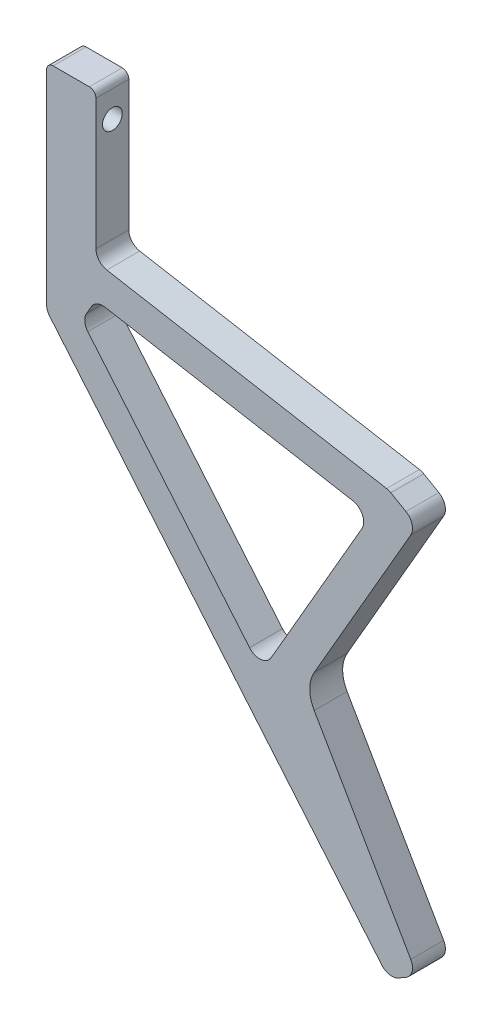
SolidWorks part; units mm, degrees
ref_plane "Front Plane" through (0, 0, 0) normal (0, 0, 1) x (1, 0, 0)
ref_plane "Top Plane" through (0, 0, 0) normal (0, 1, 0) x (1, 0, 0)
ref_plane "Right Plane" through (0, 0, 0) normal (1, 0, 0) x (0, 0, -1)
sketch "Sketch1" plane through (0, 0, 0) normal (0, 0, 1) x (1, 0, 0)
  line L0 (0, 0) -> (0, 22.413) construction
  line L9 (-5.4993, 3.175) -> (14.4086, 37.6565)
  line L10 (-57.15, 79.375) -> (-47.625, 79.375)
  line L11 (-57.15, 79.375) -> (-57.15, 37.895)
  line L13 (-47.625, 79.375) -> (-47.625, 50.8)
  line L14 (-5.4993, -3.175) -> (14.4086, -37.6565)
  line L16 (8.9094, 40.8315) -> (14.4086, 37.6565)
  line L17 (8.9094, -40.8315) -> (14.4086, -37.6565)
  line L18 (-47.625, 50.8) -> (8.9094, 40.8315)
  line L23 (0, 0) -> (-68.5179, 0) construction
  line L25 (-57.15, 37.895) -> (8.9094, -40.8315)
  arc A0 (-5.4993, 3.175) -> (-5.4993, -3.175) centre (0, 0) ccw
  point P6 (6.7742, -37.1333)
  point P15 (-57.15, 34.6569)
  dimension "D3" = 6.35
  dimension "D1" = 57.15
  dimension "D2" = 9.525
  dimension "D4" = 60
  dimension "D5" = 28.575
  dimension "D6" = 6.35
  dimension "D7" = 6.35
  dimension "D8" = 50.8
  dimension "D9" = 10
  dimension "D11" = 100
  dimension "D13" = 60
extrude "Boss-Extrude1" add sketch "Sketch1" along normal mid plane 6.35
sketch "Sketch2" plane through (-47.625, 0, 0) normal (1, 0, 0) x (0, 0, -1)
  line L0 (-3.175, 79.375) -> (3.175, 79.375) construction
  circle A0 centre (0, 73.025) radius 1.905
  point P2 (0, 79.375)
  dimension "D1" = 3.81
  dimension "D2" = 6.35
extrude "Cut-Extrude1" cut sketch "Sketch2" against normal up to surface (9.525 mm away) up to face at (-57.15, 58.635, 0)
sketch "Sketch3" plane through (0, 0, 3.175) normal (0, 0, 1) x (1, 0, 0)
  line L0 (-47.625, 44.352) -> (-50.3371, 39.6546)
  line L1 (-50.3371, 39.6546) -> (-15.6422, -1.6932)
  line L2 (-15.6422, -1.6932) -> (5.5306, 34.9793)
  line L3 (5.5306, 34.9793) -> (-47.625, 44.352)
  line L4 (-5.4993, 3.175) -> (14.4086, 37.6565) construction
  line L5 (-57.15, 37.895) -> (8.9094, -40.8315) construction
  line L6 (8.9094, 40.8315) -> (-47.625, 50.8) construction
  point P10 (-42.2435, 30.009)
  point P11 (-49.8316, 39.0522)
  point P12 (0, 0)
  point P14 (0, 0)
  dimension "D1" = 6.35
  dimension "D2" = 6.35
  dimension "D3" = 6.35
extrude "Cut-Extrude2" cut sketch "Sketch3" against normal up to surface (6.35 mm away) up to face at (-17.4763, 24.7445, -3.175)
fillet "Fillet1" radius 2.54 10 edges at (-47.625, 50.8, 0) (14.4086, 37.6565, 0) (8.9094, 40.8315, 0) (14.4086, -37.6565, 0) (8.9094, -40.8315, 0) (-57.15, 37.895, 0) (5.5306, 34.9793, 0) (-15.6422, -1.6932, 0) (-50.3371, 39.6546, 0) (-47.625, 44.352, 0)
fillet "Fillet2" radius 1.27 2 edges at (-47.625, 79.375, 0) (-57.15, 79.375, 0)
